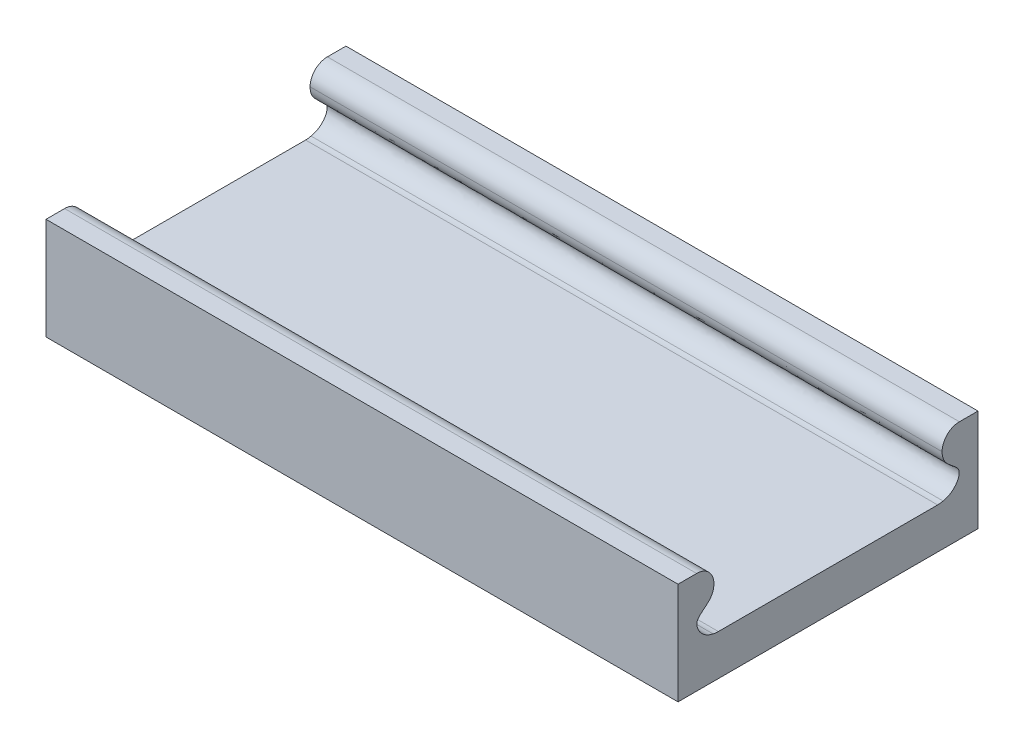
SolidWorks part; units mm, degrees
ref_plane "Front Plane" through (0, 0, 0) normal (0, 0, 1) x (1, 0, 0)
ref_plane "Top Plane" through (0, 0, 0) normal (0, 1, 0) x (1, 0, 0)
ref_plane "Right Plane" through (0, 0, 0) normal (1, 0, 0) x (0, 0, -1)
sketch "Sketch1" plane through (0, 0, 0) normal (1, 0, 0) x (0, 0, -1)
  line L0 (-23.0187, 11.9062) -> (23.0187, 11.9062) construction
  line L1 (-23.0187, 15.875) -> (0, 15.875)
  line L2 (-23.0187, 15.875) -> (-23.0188, 0)
  line L3 (-23.0188, 0) -> (23.0188, 0)
  line L4 (23.0188, 15.875) -> (23.0188, 0)
  line L5 (-15.3458, 11.9062) -> (-15.3458, 7.3025) construction
  line L6 (15.3458, 15.875) -> (15.3458, 7.3025) construction
  line L7 (0, 15.875) -> (0, 0) construction
  line L8 (-12.8058, 4.7625) -> (12.8058, 4.7625) construction
  line L9 (12.8058, 4.7625) -> (15.3458, 4.7625) construction
  line L11 (-15.3458, 15.875) -> (15.3458, 15.875)
  line L12 (-16.6158, 11.9062) -> (-15.3458, 11.9062)
  line L13 (-12.8058, 4.7625) -> (12.8058, 4.7625)
  line L14 (-16.6158, 15.875) -> (-15.3458, 15.875)
  line L15 (15.3458, 15.875) -> (16.6158, 15.875)
  line L17 (16.6158, 11.9062) -> (15.3458, 11.9062)
  line L18 (-23.0187, 11.9062) -> (-15.3458, 11.9062)
  line L19 (-15.3458, 10.871) -> (-15.3458, 11.9062)
  line L20 (15.3458, 15.875) -> (23.0188, 15.875)
  line L21 (16.6158, 11.9062) -> (23.0187, 11.9062)
  arc A0 (12.8058, 4.7625) -> (14.8932, 5.8553) centre (12.8058, 7.3025) ccw
  arc A1 (-12.8058, 4.7625) -> (-14.8932, 5.8553) centre (-12.8058, 7.3025) cw
  arc A4 (-15.3458, 11.9062) -> (-13.3282, 9.7936) centre (-15.3458, 9.8864) cw
  arc A5 (15.3458, 11.9062) -> (13.3282, 9.7936) centre (15.3458, 9.8864) ccw
  spline S1 degree 2 poles (14.8932, 5.8553) (15.6248, 7.0762) (14.3336, 7.7079) knots 0 0 0 1 1 1
  spline S2 degree 3 poles (-13.4283, 4.8409) (-13.7487, 4.8973) (-14.2862, 5.1122) (-14.9247, 5.6827) (-15.3058, 6.3217) (-15.3572, 7.1633) (-14.2239, 8.1404) (-13.334, 8.7362) (-13.326, 9.8864) knots 0 0 0 0 0.146224 0.253989 0.379668 0.474368 0.603388 1 1 1 1
  spline S3 degree 3 poles (13.4283, 4.8409) (13.7487, 4.8973) (14.2862, 5.1122) (14.9247, 5.6827) (15.3058, 6.3217) (15.3572, 7.1633) (14.2239, 8.1404) (13.334, 8.7362) (13.326, 9.8864) knots 0 0 0 0 0.146224 0.253989 0.379668 0.474368 0.603388 1 1 1 1
  point P4 (0, 0)
  point P12 (23.0188, 7.9375)
  point P15 (-15.3458, 11.9062)
  point P20 (0, 11.9062)
  dimension "D1" = 15.875
  dimension "D2" = 46.0375
  dimension "D3" = 3.9688
  dimension "D4" = 7.6729
  dimension "D5" = 7.6729
  dimension "D6" = 4.7625
extrude "Boss-Extrude1" add sketch "Sketch1" along normal blind 73.825
sketch "Sketch2" plane through (73.825, 0, 0) normal (1, 0, 0) x (0, 0, -1)
  line L0 (-23.0188, 0) -> (23.0188, 0) construction
  line L1 (-23.0188, 11.9062) -> (-17.5188, 11.9062)
  line L2 (-23.0188, 11.9062) -> (-23.0188, 0)
  line L3 (-23.0188, 0) -> (-17.5188, 0)
  line L4 (-17.5188, 11.9062) -> (-17.5188, 0)
  line L6 (23.0188, 11.9062) -> (17.5188, 11.9062)
  line L7 (23.0188, 11.9062) -> (23.0188, 0)
  line L8 (23.0188, 0) -> (17.5188, 0)
  line L9 (17.5188, 11.9062) -> (17.5188, 0)
  dimension "D1" = 5.5
  dimension "D2" = 5.5
extrude "Cut-Extrude1" cut sketch "Sketch2" against normal blind 77
equation "\"slider width\"= 1 + 13 / 16"
equation "\"slider height\"= 5 / 8"
equation "\"D1@Sketch1\"=\"slider height\""
equation "\"D2@Sketch1\"=\"slider width\""
equation "\"D3@Sketch1\"=\"slider height\"/4"
equation "\"D4@Sketch1\"=\"slider width\"/6"
equation "\"D5@Sketch1\"=\"slider width\"/6"
equation "\"D6@Sketch1\"=(\"slider height\"/4)*1.2"
